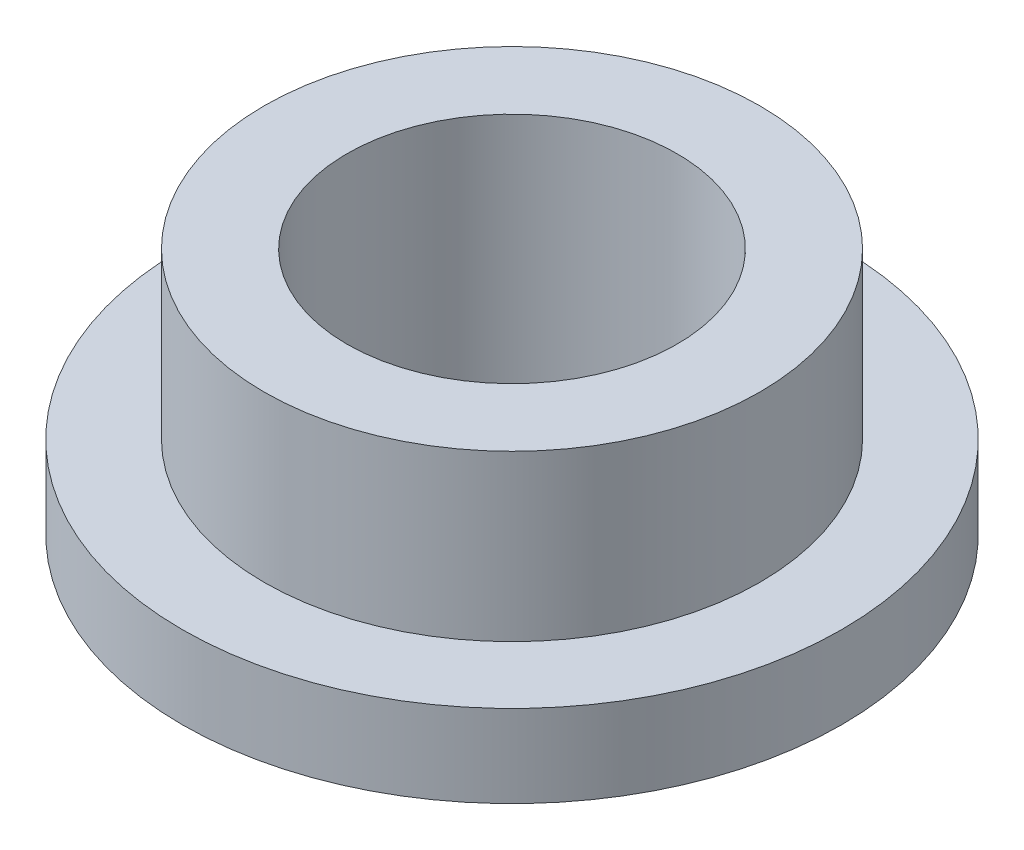
SolidWorks part; units mm, degrees
material "Commercial Bronze, UNS C22000 (90-10 Bronze)"
ref_plane "Front" through (0, 0, 0) normal (0, 0, 1) x (1, 0, 0)
ref_plane "Top" through (0, 0, 0) normal (0, 1, 0) x (1, 0, 0)
ref_plane "Right" through (0, 0, 0) normal (1, 0, 0) x (0, 0, -1)
sketch "Sketch1" plane through (0, 0, 0) normal (0, 1, 0) x (1, 0, 0)
  circle A0 centre (0, 0) radius 4.005
  circle A1 centre (0, 0) radius 6.015
  circle A2 centre (0, 0) radius 8
  dimension "ID" = 8.01
  dimension "OD" = 12.03
  dimension "FlangeOD" = 16
sketch "Sketch2" plane through (0, 0, 0) normal (0, 1, 0) x (1, 0, 0)
  circle A0 centre (0, 0) radius 4.005 construction
  circle A1 centre (0, 0) radius 6.015 construction
  circle A2 centre (0, 0) radius 4.005
  circle A3 centre (0, 0) radius 6.015
extrude "Boss-Extrude1" add sketch "Sketch2" along normal blind 6
sketch "Sketch3" plane through (0, 0, 0) normal (0, 1, 0) x (1, 0, 0)
  circle A0 centre (0, 0) radius 8 construction
  circle A1 centre (0, 0) radius 6.015 construction
  circle A2 centre (0, 0) radius 8
  circle A3 centre (0, 0) radius 6.015
extrude "Boss-Extrude2" add sketch "Sketch3" along normal blind 2
